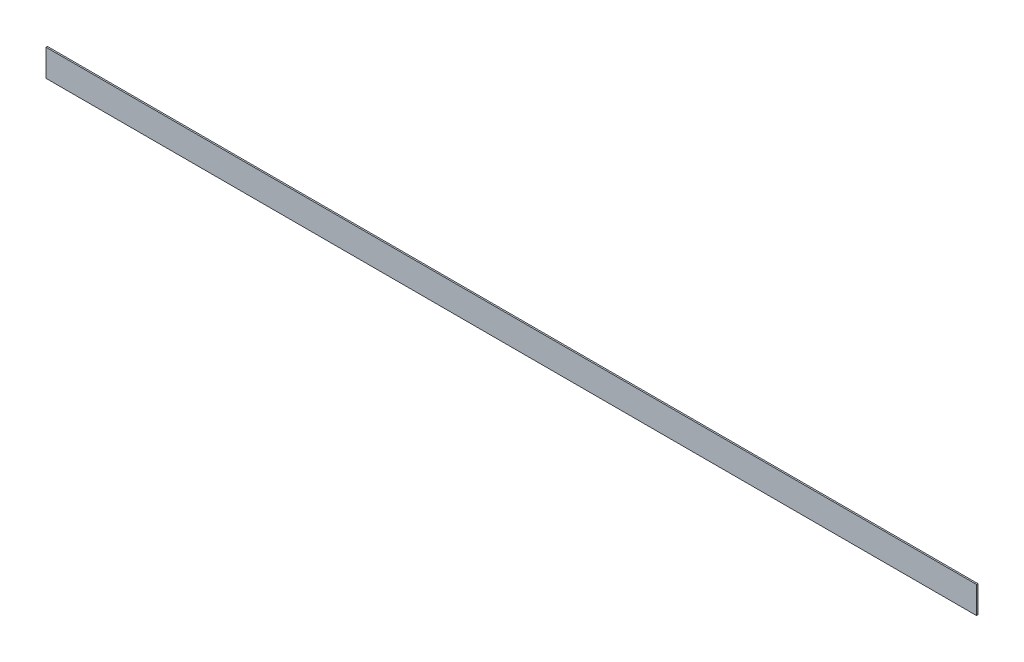
SolidWorks part; units mm, degrees
ref_plane "Front Plane" through (0, 0, 0) normal (0, 0, 1) x (1, 0, 0)
ref_plane "Top Plane" through (0, 0, 0) normal (0, 1, 0) x (1, 0, 0)
ref_plane "Right Plane" through (0, 0, 0) normal (1, 0, 0) x (0, 0, -1)
sketch "Sketch1" plane through (0, 0, 0) normal (0, 0, 1) x (1, 0, 0)
  line L1 (0, 0) -> (16560.8, 0)
  line L2 (0, 0) -> (0, -480)
  line L3 (0, -480) -> (16560.8, -480)
  line L4 (16560.8, 0) -> (16560.8, -480)
  dimension "D1" = 480
  dimension "D2" = 16560.8
extrude "Boss-Extrude1" add sketch "Sketch1" along normal blind 25.4
